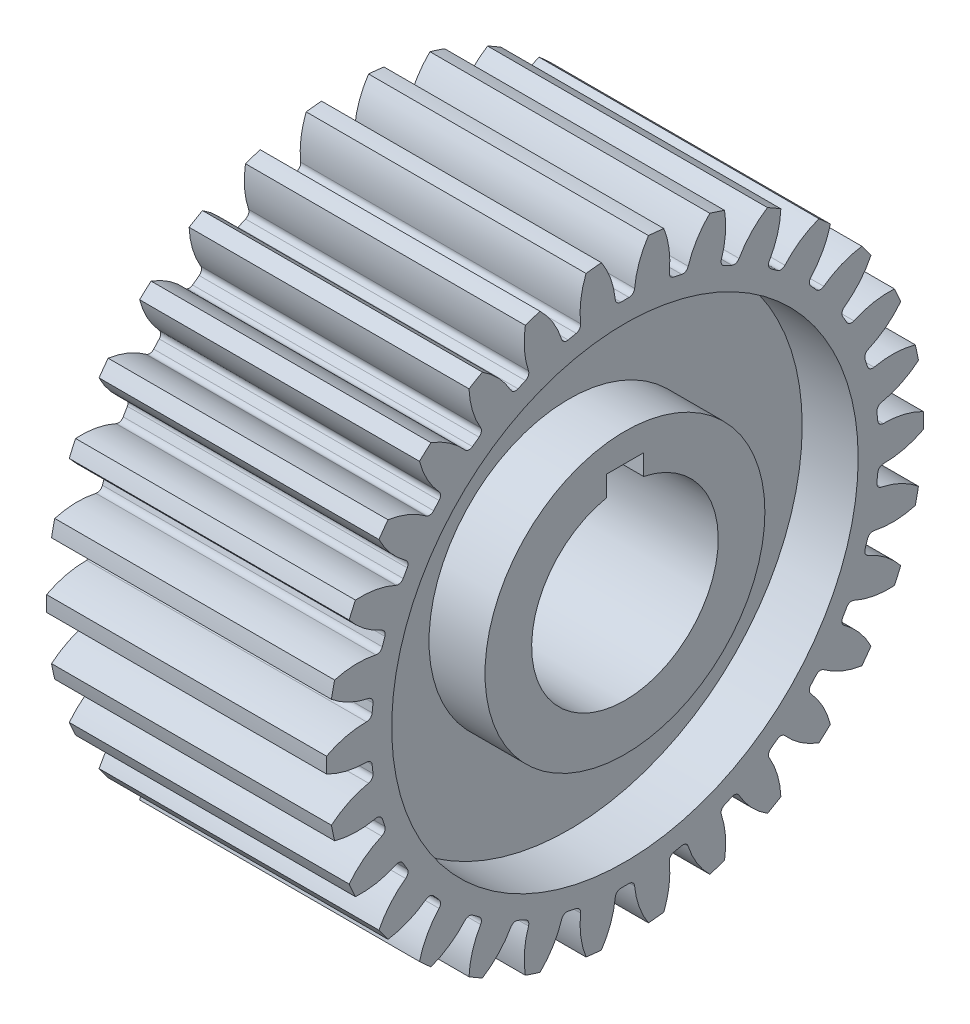
SolidWorks part; units mm, degrees
ref_plane "Front Plane" through (0, 0, 0) normal (0, 0, 1) x (1, 0, 0)
ref_plane "Top Plane" through (0, 0, 0) normal (0, 1, 0) x (1, 0, 0)
ref_plane "Right Plane" through (0, 0, 0) normal (1, 0, 0) x (0, 0, -1)
sketch "Sketch1" plane through (0, 0, 0) normal (1, 0, 0) x (0, 0, -1)
  circle A0 centre (0, 0) radius 16
  dimension "D1" = 32
extrude "Boss-Extrude1" add sketch "Sketch1" along normal mid plane 15
sketch "Sketch2" plane through (7.5, 0, 0) normal (1, 0, 0) x (0, 0, -1)
  line L1 (-1, 6) -> (1, 6)
  line L2 (-1, 6) -> (-1, 4.899)
  line L4 (1, 6) -> (1, 4.899)
  arc A0 (-1, 4.899) -> (1, 4.899) centre (0, 0) ccw
  point P3 (0, 5)
  dimension "D1" = 10
extrude "Cut-Extrude1" cut sketch "Sketch2" against normal through all
sketch "Sketch3" plane through (7.5, 0, 0) normal (1, 0, 0) x (0, 0, -1)
  circle A0 centre (0, 0) radius 7.5
  circle A1 centre (0, 0) radius 12.5
  dimension "D1" = 25
  dimension "D2" = 15
extrude "Cut-Extrude2" cut sketch "Sketch3" against normal blind 3
mirror "Mirror1" about plane through (0, 0, 0) normal (1, 0, 0) of "Cut-Extrude2"
sketch "Sketch4" plane through (7.5, 0, 0) normal (1, 0, 0) x (0, 0, -1)
  line L0 (0, 0) -> (0, 17.9992) construction
  line L1 (-0.2199, 13.6) -> (0.2199, 13.6) construction
  line L2 (-0.2199, 13.6) -> (0.2199, 13.6)
  arc A0 (0.5184, 13.8707) -> (2.08, 16.88) centre (5.0567, 13.4256) cw
  arc A1 (-0.5184, 13.8707) -> (-2.08, 16.88) centre (-5.0567, 13.4256) ccw
  arc A2 (-2.08, 16.88) -> (2.08, 16.88) centre (0, -0.9994) cw
  arc A3 (-0.5184, 13.8707) -> (-0.2199, 13.6) centre (-0.2199, 13.9) ccw
  arc A4 (0.2199, 13.6) -> (0.5184, 13.8707) centre (0.2199, 13.9) ccw
  point P8 (0, 13.6)
  point P13 (-0.5, 13.6)
  point P16 (0.5, 13.6)
  dimension "D5" = 4.56
  dimension "D6" = 18
  dimension "D7" = 0.3
  dimension "D1" = 0.5
  dimension "D2" = 13.6
  dimension "D3" = 1.58
  dimension "D4" = 3.28
extrude "Cut-Extrude3" cut sketch "Sketch4" against normal through all
pattern_circular "CirPattern1" count 30 over 360 about axis through (0, 0, 0) along (1, 0, 0) of "Cut-Extrude3"
